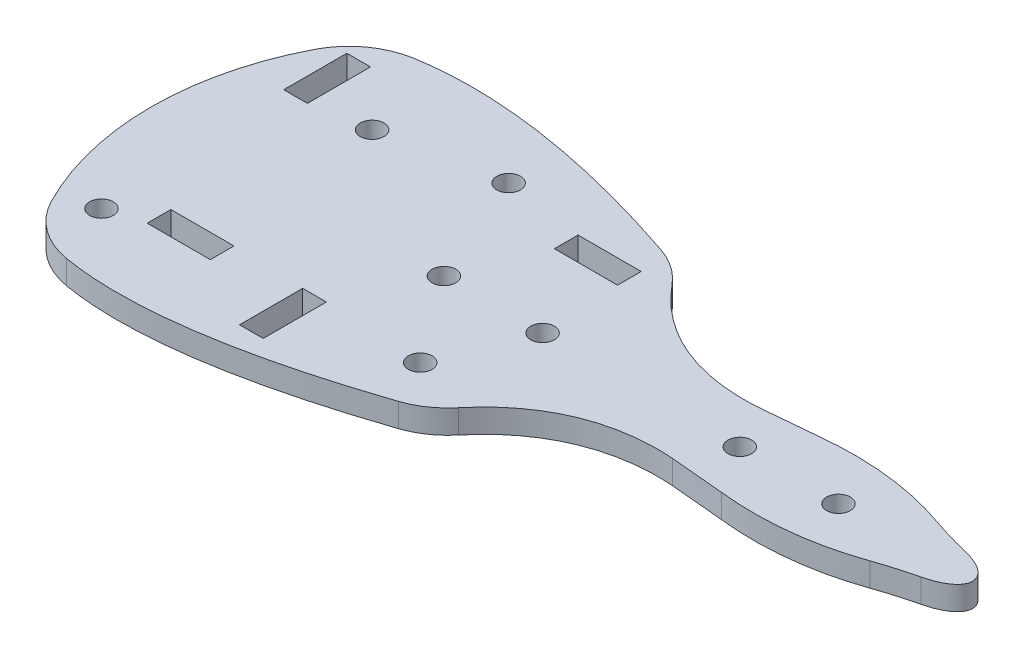
SolidWorks part; units mm, degrees
ref_plane "Plano frontal" through (0, 0, 0) normal (0, 0, 1) x (1, 0, 0)
ref_plane "Plano superior" through (0, 0, 0) normal (0, 1, 0) x (1, 0, 0)
ref_plane "Plano direito" through (0, 0, 0) normal (1, 0, 0) x (0, 0, -1)
sketch "Esboço1" plane through (0, 0, 0) normal (0, 1, 0) x (1, 0, 0)
  line L4 (-46.742, -10.7001) -> (-43.742, -10.7001)
  line L5 (-43.742, -10.7001) -> (-43.742, -18.7001)
  line L6 (-43.742, -18.7001) -> (-46.742, -18.7001)
  line L7 (-46.742, -18.7001) -> (-46.742, -10.7001)
  line L8 (-66.742, 9.8999) -> (-69.742, 9.8999)
  line L9 (-69.742, 9.8999) -> (-69.742, 17.8999)
  line L10 (-69.742, 17.8999) -> (-66.742, 17.8999)
  line L11 (-66.742, 17.8999) -> (-66.742, 9.8999)
  line L12 (-35.142, 9.5999) -> (-35.142, 12.5999)
  line L13 (-35.142, 12.5999) -> (-27.142, 12.5999)
  line L14 (-27.142, 12.5999) -> (-27.142, 9.5999)
  line L15 (-27.142, 9.5999) -> (-35.142, 9.5999)
  line L16 (-55.742, -10.4001) -> (-55.742, -13.4001)
  line L17 (-55.742, -13.4001) -> (-63.742, -13.4001)
  line L18 (-63.742, -13.4001) -> (-63.742, -10.4001)
  line L19 (-63.742, -10.4001) -> (-55.742, -10.4001)
  line L43 (-4.6744, 5.1268) -> (2.1565, 5.7499)
  line L44 (2.1565, -6.5501) -> (-4.6744, -5.927)
  circle A2 centre (-45.242, 13.8999) radius 1.5
  circle A3 centre (-68.242, -14.7001) radius 1.5
  circle A4 centre (-59.742, 11.0999) radius 1.5
  circle A5 centre (-31.142, -11.4018) radius 1.5
  arc A9 (-72.1928, 16.3196) -> (-72.1928, -17.1198) centre (-39.8393, -0.4001) ccw
  arc A10 (-72.1928, 16.3196) -> (-64.9861, 21.587) centre (-63.309, 11.7286) cw
  arc A14 (24.1011, 2.407) -> (19.1277, 3.8594) centre (35.6119, 51.064) cw
  arc A15 (19.1277, -4.6595) -> (24.1011, -3.2071) centre (35.6119, -51.8641) cw
  circle A24 centre (-39.142, -0.4001) radius 1.5
  circle A25 centre (10.858, -0.4001) radius 1.5
  circle A26 centre (-1.642, -0.4001) radius 1.5
  circle A27 centre (-26.642, -0.4001) radius 1.5
  arc A29 (-72.1928, -17.1198) -> (-64.9861, -22.3871) centre (-63.309, -12.5288) ccw
  arc A30 (-28.2773, -17.0396) -> (-23.759, -13.9261) centre (-31.4747, -7.5646) ccw
  arc A31 (-28.2773, 16.2395) -> (-23.759, 13.1259) centre (-31.4747, 6.7644) cw
  ellipse E0 centre (20.858, -0.4001) end of major axis (27.858, -0.4001) minor radius 3.1675 (24.1011, -3.2071) -> (24.1011, 2.407) ccw
  spline S0 degree 3 poles (19.1277, 3.8594) (13.6929, 5.7573) (8.0358, 6.3875) (2.1565, 5.7499) knots 0.353889 0.353889 0.353889 0.353889 1 1 1 1
  spline S2 degree 3 poles (-28.2773, 16.2395) (-34.5792, 18.3661) (-47.5978, 21.9476) (-59.6503, 22.4947) (-64.9861, 21.587) knots 0.24159 0.24159 0.24159 0.24159 0.401358 0.561127 0.561127 0.561127 0.561127
  spline S3 degree 3 poles (-28.2773, -17.0396) (-34.5792, -19.1662) (-47.5978, -22.7477) (-59.6503, -23.2949) (-64.9861, -22.3871) knots 0.24159 0.24159 0.24159 0.24159 0.401358 0.561127 0.561127 0.561127 0.561127
  spline S5 degree 3 poles (19.1277, -4.6595) (13.6929, -6.5574) (8.0358, -7.1876) (2.1565, -6.5501) knots 0.353889 0.353889 0.353889 0.353889 1 1 1 1
  spline S9 degree 3 poles (-23.759, 13.1259) (-18.9931, 7.3456) (-12.4241, 4.5674) (-4.6744, 5.1268) knots 0.101822 0.101822 0.101822 0.101822 1 1 1 1
  spline S10 degree 3 poles (-23.759, -13.9261) (-18.9931, -8.1457) (-12.4241, -5.3676) (-4.6744, -5.927) knots 0.101822 0.101822 0.101822 0.101822 1 1 1 1
  dimension "D1" = 10
  dimension "D2" = 10
  dimension "D5" = 10
extrude "Ressalto-extrusão1" add sketch "Esboço1" along normal blind 3
